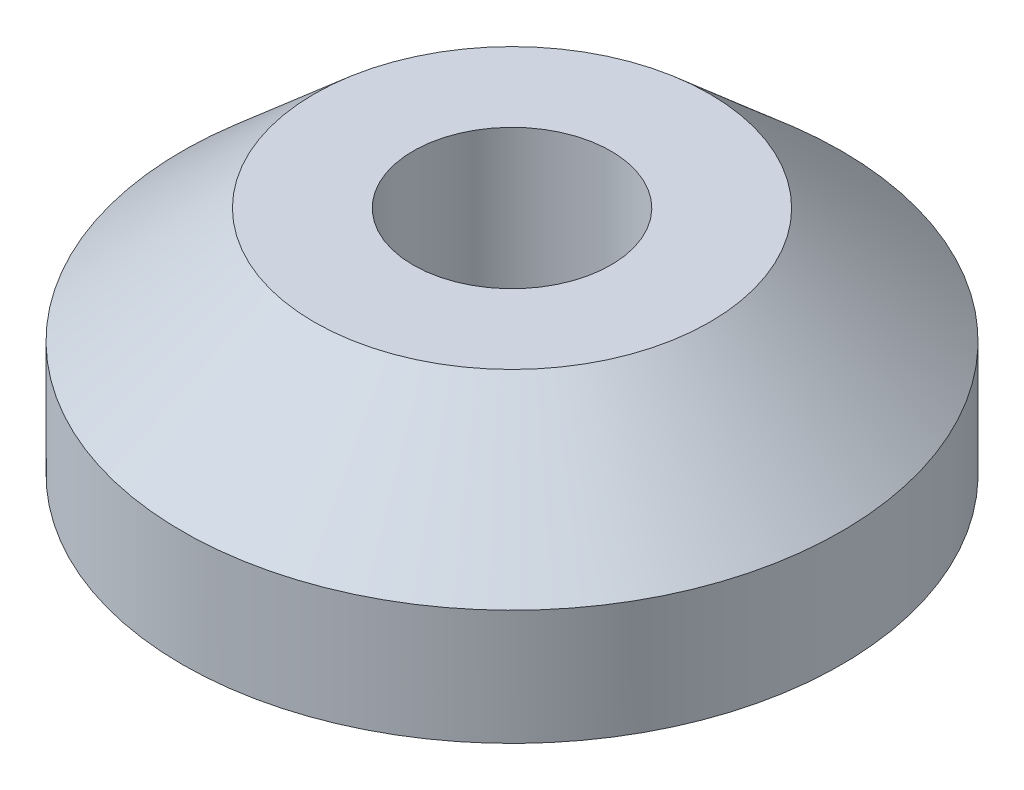
SolidWorks part; units mm, degrees
ref_plane "Front Plane" through (0, 0, 0) normal (0, 0, 1) x (1, 0, 0)
ref_plane "Top Plane" through (0, 0, 0) normal (0, 1, 0) x (1, 0, 0)
ref_plane "Right Plane" through (0, 0, 0) normal (1, 0, 0) x (0, 0, -1)
sketch "Sketch1" plane through (0, 0, 0) normal (0, 1, 0) x (1, 0, 0)
  circle A0 centre (0, 0) radius 6
ref_plane "Plane1" through (0, -7, 0) normal (0, 1, 0) x (1, 0, 0)
sketch "Sketch2" plane through (0, -7, 0) normal (0, 1, 0) x (1, 0, 0)
  circle A0 centre (0, 0) radius 10
extrude "Boss-Extrude1" add sketch "Sketch2" along normal blind 3.5
loft "Loft1" add profiles "Sketch1" section "Sketch1" section face at (0, -3.5, 10)
sketch "Sketch3" plane through (0, 0, 0) normal (0, 1, 0) x (1, 0, 0)
  circle A0 centre (0, 0) radius 3
extrude "Cut-Extrude1" cut sketch "Sketch3" against normal blind 9.5
